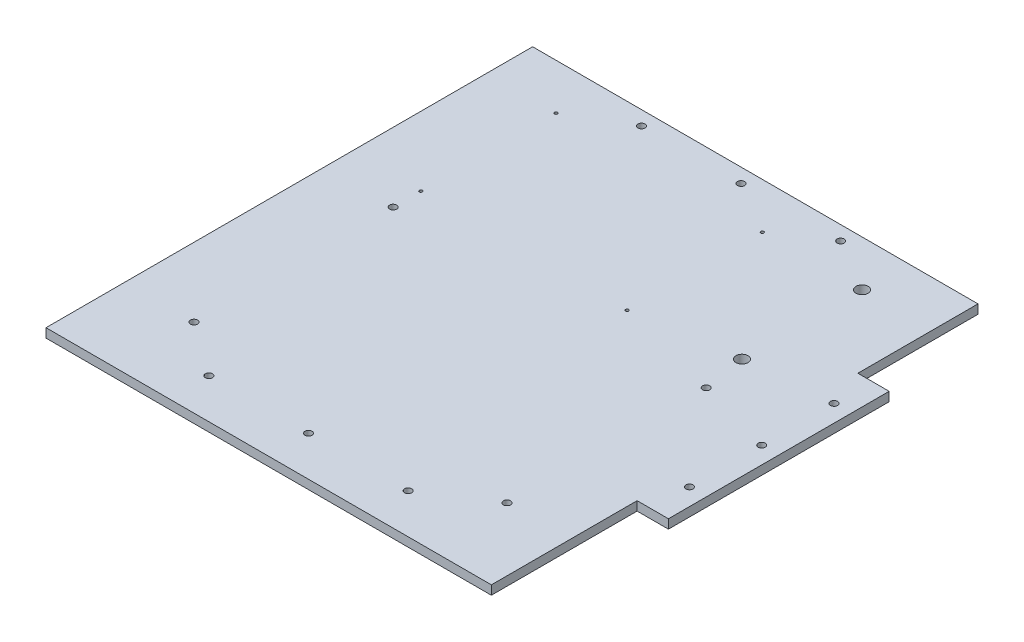
SolidWorks part; units mm, degrees
material "Cedar"
ref_plane "Front Plane" through (0, 0, 0) normal (0, 0, 1) x (1, 0, 0)
ref_plane "Top Plane" through (0, 0, 0) normal (0, 1, 0) x (1, 0, 0)
ref_plane "Right Plane" through (0, 0, 0) normal (1, 0, 0) x (0, 0, -1)
sketch "Sketch1" plane through (0, 0, 0) normal (0, 1, 0) x (1, 0, 0)
  line L0 (72.8376, -16.2766) -> (72.8376, -52.4668) construction
  line L1 (-156.5, -171) -> (156.5, -171)
  line L2 (-156.5, -171) -> (-156.5, 171)
  line L3 (-156.5, 171) -> (156.5, 171)
  line L4 (156.5, -171) -> (156.5, 171)
  line L5 (-156.5, -171) -> (156.5, 171) construction
  line L6 (-156.5, 171) -> (156.5, -171) construction
  point P0 (0, 0)
  dimension "D1" = 342
  dimension "D2" = 313
extrude "Boss-Extrude1" add sketch "Sketch1" against normal blind 6.35
ref_plane "Plane1" through (0, 0, -9) normal (0, 0, -1) x (-1, 0, 0)
sketch "Sketch3" plane through (0, 0, 0) normal (0, 1, 0) x (1, 0, 0)
  line L0 (156.5, 9) -> (-156.5, 9) construction
  line L1 (156.5, -171) -> (156.5, 171) construction
  line L2 (-156.5, 171) -> (-156.5, -171) construction
  line L3 (55, 9) -> (-55, 9) construction
  line L4 (156.5, 86.5702) -> (156.5, -68.5702)
  line L5 (156.5, -68.5702) -> (178.5, -68.5702)
  line L6 (178.5, -68.5702) -> (178.5, 86.5702)
  line L7 (178.5, 86.5702) -> (156.5, 86.5702)
  circle A0 centre (166.5, 9) radius 2.5
  circle A1 centre (166.5, -41.8) radius 2.5
  circle A2 centre (166.5, 59.8) radius 2.5
  point P10 (156.5, 9)
  dimension "D2" = 5
  dimension "D4" = 5
  dimension "D5" = 50.8
  dimension "D1" = 22
  dimension "D3" = 10
extrude "Boss-Extrude2" add sketch "Sketch3" against normal blind 6.35
sketch "Sketch2" plane through (0, 0, 0) normal (0, 1, 0) x (1, 0, 0)
  line L0 (156.5, 9) -> (-156.5, 9) construction
  line L1 (156.5, -171) -> (156.5, -68.5702) construction
  line L2 (-156.5, 171) -> (-156.5, -171) construction
  line L3 (0, -143) -> (0, -171) construction
  line L4 (55, 9) -> (-55, 9) construction
  line L5 (156.5, -143) -> (-156.5, -143) construction
  line L6 (-156.5, -171) -> (156.5, -171) construction
  circle A0 centre (0, -143) radius 2.5
  circle A1 centre (-70, -143) radius 2.5
  circle A2 centre (70, -143) radius 2.5
  circle A3 centre (-70, 161) radius 2.5
  circle A4 centre (0, 161) radius 2.5
  circle A5 centre (70, 161) radius 2.5
  dimension "D2" = 5
  dimension "D3" = 5
  dimension "D4" = 70
  dimension "D1" = 152
extrude "Cut-Extrude1" cut sketch "Sketch2" against normal through all
sketch "Sketch4" plane through (0, 0, 0) normal (0, 1, 0) x (1, 0, 0)
  line L0 (-107.9115, 138.8296) -> (-107.9115, 47.3226) construction
  line L1 (37.0885, 43.8296) -> (-107.9115, 43.8296) construction
  circle A15 centre (107.2049, 138.8296) radius 4.25
  circle A16 centre (107.2049, 54.4254) radius 4.25
  circle A17 centre (-107.9115, -115.6055) radius 2.5
  circle A18 centre (-107.9115, 24.3945) radius 2.5
  circle A19 centre (112.0885, 24.3945) radius 2.5
  circle A20 centre (112.0885, -115.6055) radius 2.5
  circle A21 centre (-107.9115, 138.8296) radius 1.05
  circle A22 centre (37.0885, 138.8296) radius 1.05
  circle A23 centre (37.0885, 43.8296) radius 1.05
  circle A24 centre (-107.9115, 43.8296) radius 1.05
  dimension "D1" = 2.1
extrude "Cut-Extrude2" cut sketch "Sketch4" against normal through all
